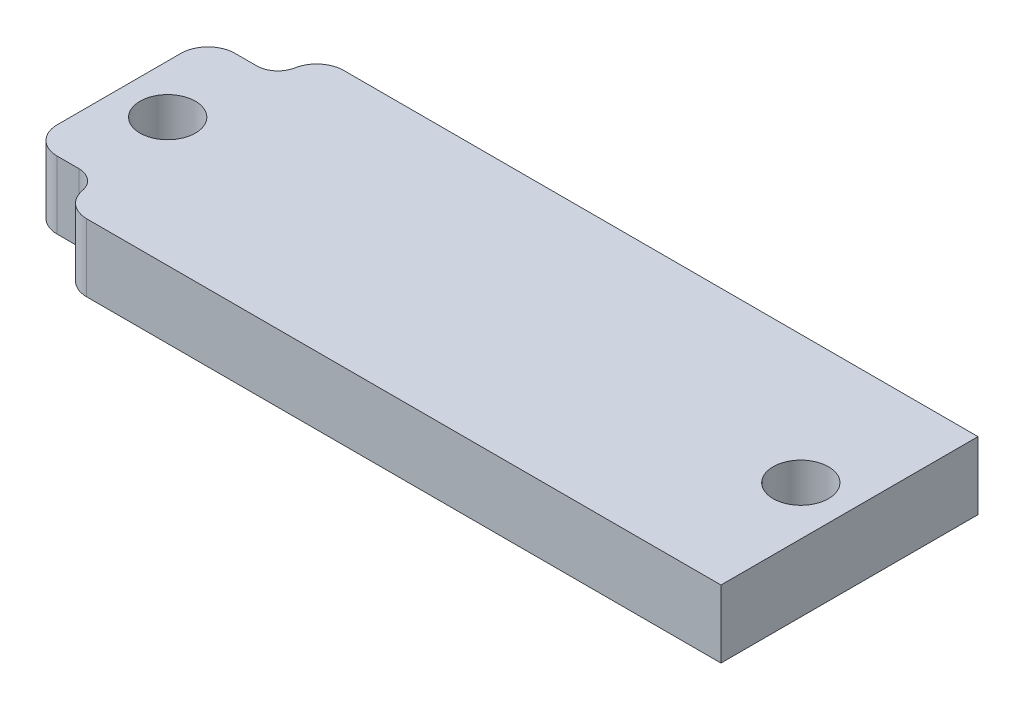
SolidWorks part; units mm, degrees
ref_plane "Front Plane" through (0, 0, 0) normal (0, 0, 1) x (1, 0, 0)
ref_plane "Top Plane" through (0, 0, 0) normal (0, 1, 0) x (1, 0, 0)
ref_plane "Right Plane" through (0, 0, 0) normal (1, 0, 0) x (0, 0, -1)
sketch "Sketch2" plane through (0, 0, 0) normal (0, 1, 0) x (1, 0, 0)
  line L1 (0, 0) -> (68.58, 0)
  line L2 (0, 0) -> (0, 24.13)
  line L3 (0, 24.13) -> (68.58, 24.13)
  line L4 (68.58, 0) -> (68.58, 24.13)
  circle A0 centre (4.57, 12.065) radius 2.6
  circle A1 centre (64.01, 12.065) radius 2.6
  point P10 (68.58, 12.065)
  dimension "D4" = 5.2
  dimension "D1" = 68.58
  dimension "D2" = 24.13
  dimension "D3" = 4.57
  dimension "D5" = 4.57
extrude "Boss-Extrude1" add sketch "Sketch2" along normal blind 6.35
sketch "Sketch3" plane through (0, 6.35, 0) normal (0, 1, 0) x (1, 0, 0)
  line L0 (6.57, 22.415) -> (6.57, 24.13)
  line L2 (4.57, 20.415) -> (0, 20.415)
  line L3 (0, 24.13) -> (0, 0) construction
  line L4 (68.58, 24.13) -> (0, 24.13) construction
  line L5 (4.57, 12.065) -> (64.01, 12.065) construction
  line L6 (34.29, 24.13) -> (34.29, 0) construction
  line L7 (0, 0) -> (68.58, 0) construction
  line L8 (6.57, 1.715) -> (6.57, 0)
  line L9 (4.57, 3.715) -> (0, 3.715)
  arc A0 (4.57, 20.415) -> (6.57, 22.415) centre (4.57, 22.415) ccw
  circle A1 centre (4.57, 12.065) radius 2.6 construction
  circle A2 centre (4.57, 12.065) radius 2.6
  arc A3 (4.57, 3.715) -> (6.57, 1.715) centre (4.57, 1.715) cw
  line M1 (0, 0) -> (68.58, 0)
  line M5 (68.58, 24.13) -> (0, 24.13)
  line M7 (0, 24.13) -> (0, 0)
  dimension "D1" = 10.35
  dimension "D2" = 4
extrude "Cut-Extrude1" cut sketch "Sketch3" against normal through all contours A3 L9 L8 M7 M1 | L2 A0 L0 M5 M7
fillet "Fillet3" radius 2.54 4 edges at (6.57, 3.175, 0) (0, 3.175, -3.715) (0, 3.175, -20.415) (6.57, 3.175, -24.13)
sketch "Sketch4" plane through (0, 0, 0) normal (0, -1, 0) x (1, 0, 0)
  line L0 (0, -12.065) -> (68.58, -12.065) construction
  line L1 (0, -17.875) -> (0, -6.255) construction
  line L2 (68.58, 0) -> (68.58, -24.13) construction
  circle A0 centre (34.29, -12.065) radius 4
  point P8 (34.29, -12.065)
  dimension "D1" = 8
